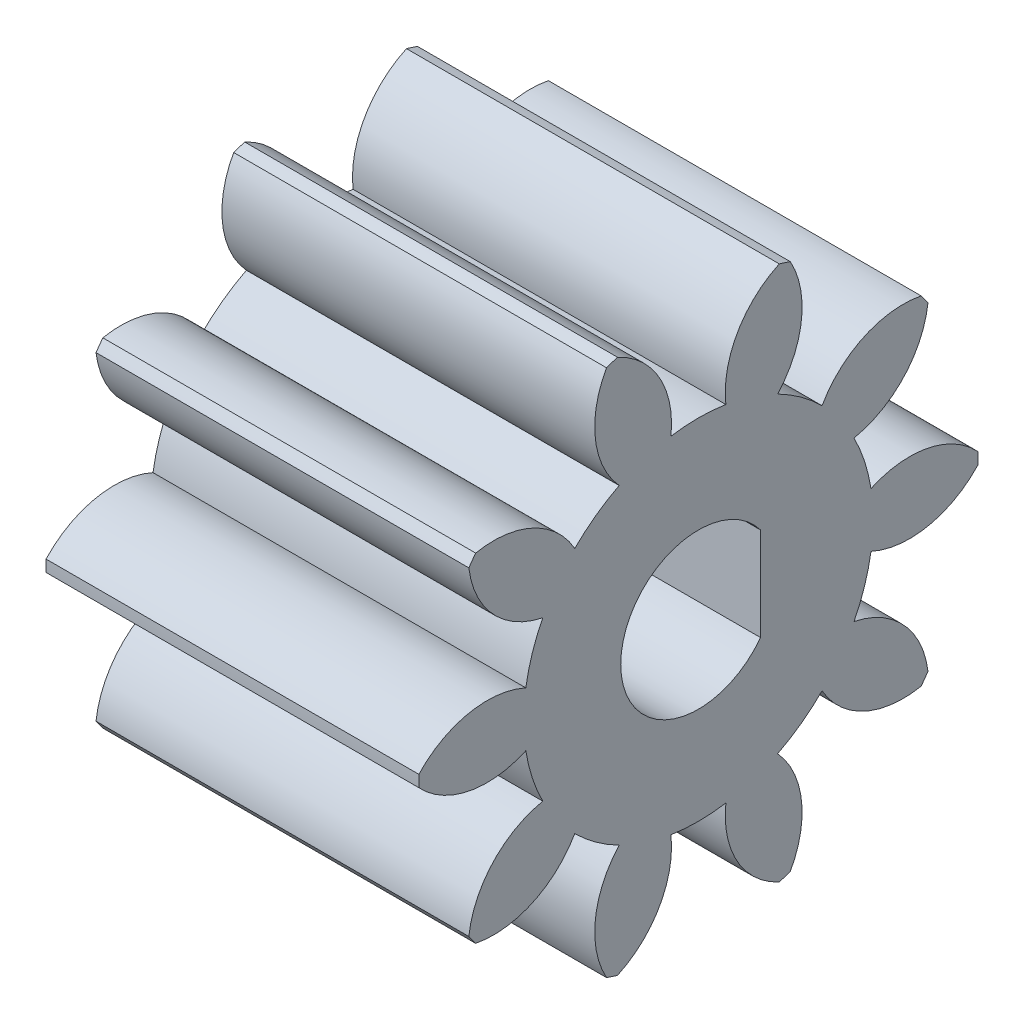
SolidWorks part; units mm, degrees
ref_plane "Plane1" through (0, 0, 0) normal (0, 0, 1) x (1, 0, 0)
ref_plane "Plane2" through (0, 0, 0) normal (0, 1, 0) x (1, 0, 0)
ref_plane "Plane3" through (0, 0, 0) normal (1, 0, 0) x (0, 0, -1)
sketch "HoldingSke" plane through (0, 0, 0) normal (0, 1, 0) x (1, 0, 0)
  line L0 (0, 0) -> (0.6565, -0.1158)
  line L1 (-15, 0) -> (100, 0) construction
  line L2 (0, 0) -> (-2.1039, 2.3779)
  line L3 (0, 0) -> (-11.863, 4.5341)
  line L4 (0, 0) -> (8.5048, 1.4996)
  line L5 (0, 0) -> (-46.8476, -17.4728)
  line L6 (0, 0) -> (-9.9476, -6.7116)
  line L7 (-2.1039, 2.3779) -> (8.6586, 51.2059)
  line L8 (-76.2, 54.61) -> (-75.5, 54.61)
  line L9 (-71.009, 38.7566) -> (-53.1078, 45.2721)
  line L10 (-76.2, 71.12) -> (104.1128, 71.12)
  line L11 (0, 0) -> (-12, 0)
  line L12 (-76.2, 101.6) -> (-76.147, 101.6)
  line L13 (24.9733, 27.94) -> (52.9518, 28.4284)
  line L14 (24.9733, 27.94) -> (24.9743, 27.94)
  line L15 (24.9733, 27.94) -> (100.4006, 29.5858)
  line L16 (-63.627, -1.5) -> (-12.827, -1.5)
  circle A0 centre (0, 0) radius 2
  circle A1 centre (0, 0) radius 5.624
  circle A2 centre (0, 0) radius 37.5
  circle A3 centre (0, 0) radius 2
  dimension "MHD" = 11.248
  dimension "Hub_dia" = 75
  dimension "Bore" = 4
  dimension "MBD" = 4
  dimension "Num_teeth" = 10
  dimension "Pitch" = 0.6667
  dimension "Overall_len" = 50
  dimension "Show_teeth" = 10
  dimension "Thickness" = 12
  dimension "OAL" = 50.0001
  dimension "T_dim" = 0.7
  dimension "Ap" = 20
  dimension "H" = 19.05
  dimension "Pitch_radius" = 180.3128
  dimension "Width" = 12
  dimension "Backlash" = 0.053
  dimension "Addendum_fac" = 1
  dimension "Dedendum_fac" = 1.25
  dimension "Clearance_fac" = 0.25
  dimension "Dedendum_add" = 0.001
  dimension "Module" = 1.5
sketch "BasProSke" plane through (0, 0, 0) normal (0, 1, 0) x (1, 0, 0)
  line L0 (-10, 0) -> (60, 0) construction
  line L1 (0, 0) -> (0, 9)
  line L2 (0, 0) -> (12, 0)
  line L3 (12, 0) -> (12, 9)
  line L4 (12, 9) -> (0, 9)
  dimension "Thickness" = 12
  dimension "Diameter" = 18
revolve "Base-Revolve" add sketch "BasProSke" angle 360 about L0
sketch "TooCutSke" plane through (0, 0, 0) normal (1, 0, 0) x (0, 0, -1)
  line L1 (0, 0) -> (0, 107) construction
  line L2 (0, 0) -> (-1.2658, 7.3924) construction
  line L3 (0, 0) -> (-4.5869, 14.117) construction
  line L4 (-1.2658, 7.3924) -> (-2.2934, 7.0585) construction
  arc A0 (0.8839, 5.5541) -> (-0.8839, 5.5541) centre (0, 0) ccw
  arc A1 (2.6378, 8.6313) -> (-2.6378, 8.6313) centre (0, 0) ccw
  circle A2 centre (0, 0) radius 7.5 construction
  circle A3 centre (0, 0) radius 7.0477 construction
  arc A4 (-0.8839, 5.5541) -> (-2.6378, 8.6313) centre (-3.8646, 5.8936) ccw
  arc A5 (2.6378, 8.6313) -> (0.8839, 5.5541) centre (3.8646, 5.8936) ccw
  dimension "Root_dia" = 11.248
  dimension "Overcut_dia" = 18.0508
  dimension "Pitch_dia" = 15
  dimension "Base_dia" = 14.0954
  dimension "Flank_rad" = 3
  dimension "Half_ang" = 18
  dimension "Half_CT" = 1.0805
extrude "ToothCut" cut sketch "TooCutSke" along normal through all
fillet "Breaks" [suppressed] radius 0.03
fillet "RootFillets" [suppressed] radius 0.376
pattern_circular "TeethCuts" count 10 every 36 about axis through (-10, 0, 0) along (1, 0, 0) of "ToothCut", "RootFillets", "Breaks"
sketch "HubNeaOneSke" plane through (0, 0, 0) normal (-1, 0, 0) x (0, 0, 1)
  circle A0 centre (0, 0) radius 5.624
  dimension "Diameter" = 11.248
extrude "HubNearOne" [suppressed] add sketch "HubNeaOneSke" along normal blind 38.0001
sketch "HubNeaBotSke" plane through (0, 0, 0) normal (-1, 0, 0) x (0, 0, 1)
  circle A0 centre (0, 0) radius 5.624
  dimension "Diameter" = 11.248
extrude "HubNearBoth" [suppressed] add sketch "HubNeaBotSke" along normal blind 19
ref_plane "FarPln" through (12, 0, 0) normal (1, 0, 0) x (0, 0, -1)
sketch "HubFarSke" plane through (12, 0, 0) normal (1, 0, 0) x (0, 0, -1)
  circle A0 centre (0, 0) radius 5.624
  dimension "Diameter" = 11.248
extrude "HubFar" [suppressed] add sketch "HubFarSke" along normal blind 19
sketch "BorSke" plane through (0, 0, 0) normal (1, 0, 0) x (0, 0, -1)
  circle A0 centre (0, 0) radius 2
  dimension "Diameter" = 4
extrude "Bore" cut sketch "BorSke" along normal mid plane 100.0001
sketch "KeySke" plane through (0, 0, 0) normal (1, 0, 0) x (0, 0, -1)
  line L0 (-0.8, 0) -> (-0.8, 2.7)
  line L1 (-0.8, 2.7) -> (0.8, 2.7)
  line L2 (0.8, 2.7) -> (0.8, 0)
  line L3 (0, 0) -> (0, 34) construction
  line L4 (-0.8, 0) -> (0.8, 0)
  dimension "Offset" = 2.7
  dimension "Width" = 1.6
extrude "Keyway" [suppressed] cut sketch "KeySke" along normal mid plane 100.0001
pattern_circular "Keyway2" [suppressed] count 2 every 90 about axis through (-10, 0, 0) along (1, 0, 0)
sketch "Sketch1" plane through (12, 0, 0) normal (1, 0, 0) x (0, 0, -1)
  line L0 (2, 1.5) -> (2, -1.5)
  line L1 (-2.5, 0) -> (-2.5, -13.2605) construction
  line L2 (-2.5, -13.2605) -> (-2.5, 14.3098) construction
  arc A0 (2, 1.5) -> (2, -1.5) centre (0, 0) ccw
  point P7 (0, 0)
  point P8 (-2.5, 0)
  point P9 (0, 0)
  dimension "D1" = 5
  dimension "D2" = 4.5
extrude "Cut-Extrude1" cut sketch "Sketch1" against normal blind 18
equation "' \"Module@HoldingSke\" = 6.35"
equation "' \"Num_teeth@HoldingSke\" = 12"
equation "' \"Ap@HoldingSke\" =  20"
equation "' \"Ap@HoldingSke\" = 20"
equation "' \"Width@HoldingSke\" = 0.5 * 25.4"
equation "' \"Hub_dia@HoldingSke\"= 1 * 25.4"
equation "' \"Hub_dia@HoldingSke\" = 1 * 25.4"
equation "' \"Overall_len@HoldingSke\" = 1.0 * 25.4"
equation "' \"Bore@HoldingSke\" = 0.75 * 25.4"
equation "' \"T_dim@HoldingSke\" = 0.1 * 25.4"
equation "' \"Width@KeySke\" = 0.25 * 25.4"
equation "' \"Show_teeth@HoldingSke\" = 13"
equation "' \"Backlash@HoldingSke\" = 0.009 * 25.4"
equation "' \"Addendum_fac@HoldingSke\" = 1.0"
equation "' \"Dedendum_fac@HoldingSke\" = 1.25"
equation "' \"Dedendum_add@HoldingSke\" = 0.00005 * 25.4"
equation "' \"Clearance_fac@HoldingSke\" = 0.25"
equation "\"Pitch@HoldingSke\" = 1 / \"Module@HoldingSke\""
equation "\"Overcut_dia@TooCutSke\" = (\"Num_teeth@HoldingSke\" + 2 * \"Addendum_fac@HoldingSke\") / \"Pitch@HoldingSke\" + 0.002 * 25.4"
equation "\"Pitch_dia@TooCutSke\" = \"Num_teeth@HoldingSke\" / \"Pitch@HoldingSke\""
equation "\"Base_dia@TooCutSke\" = \"Num_teeth@HoldingSke\" / \"Pitch@HoldingSke\" * cos((\"Ap@HoldingSke\"  * 3.14159265 / 180))"
equation "\"Root_dia@TooCutSke\" = (\"Num_teeth@HoldingSke\" + 2) / \"Pitch@HoldingSke\" - 2 * (\"Addendum_fac@HoldingSke\" + \"Dedendum_fac@HoldingSke\") / \"Pitch@HoldingSke\" - \"Dedendum_add@HoldingSke\" * 2"
equation "\"Half_ang@TooCutSke\" = 180 / \"Num_teeth@HoldingSke\""
equation "\"Half_CT@TooCutSke\" = \"Num_teeth@HoldingSke\" / \"Pitch@HoldingSke\" * sin((3.14159265 / 2 / \"Num_teeth@HoldingSke\")) / 2 - 7 * \"Backlash@HoldingSke\" / 4"
equation "\"Flank_rad@TooCutSke\" = \"Num_teeth@HoldingSke\" / \"Pitch@HoldingSke\" / 5"
equation "\"Radius@RootFillets\" = \"Clearance_fac@HoldingSke\" / \"Pitch@HoldingSke\" + \"Dedendum_add@HoldingSke\""
equation "\"Break_rad@Breaks\" = 0.02 / \"Pitch@HoldingSke\""
equation "\"Thickness@HoldingSke\" = \"Width@HoldingSke\""
equation "\"OAL@HoldingSke\" = \"Thickness@HoldingSke\""
equation "\"MHD@HoldingSke\" = (\"Num_teeth@HoldingSke\" + 2) / \"Pitch@HoldingSke\" - 2 * (\"Addendum_fac@HoldingSke\" + \"Dedendum_fac@HoldingSke\")  / \"Pitch@HoldingSke\" - \"Dedendum_add@HoldingSke\" * 2"
equation "\"MBD@HoldingSke\" = (\"Num_teeth@HoldingSke\" + 2) / \"Pitch@HoldingSke\" - 2 * (\"Addendum_fac@HoldingSke\" + \"Dedendum_fac@HoldingSke\")  / \"Pitch@HoldingSke\" - \"Dedendum_add@HoldingSke\" * 2 - 0.002 * 25.4"
equation "\"MHD@HoldingSke\" = ((sgn( \"MHD@HoldingSke\" - \"Hub_dia@HoldingSke\" )-1)*( \"MHD@HoldingSke\" - \"Hub_dia@HoldingSke\" ))/-2+ \"Hub_dia@HoldingSke\""
equation "\"MBD@HoldingSke\" = ((sgn( \"MBD@HoldingSke\" - \"Bore@HoldingSke\" )-1)*( \"MBD@HoldingSke\" - \"Bore@HoldingSke\" ))/-2+ \"Bore@HoldingSke\""
equation "\"OAL@HoldingSke\" = ((sgn( \"OAL@HoldingSke\" - \"Overall_len@HoldingSke\" )+1)*( \"OAL@HoldingSke\" - \"Overall_len@HoldingSke\" ))/2 + \"Overall_len@HoldingSke\" + 0.000002 * 25.4"
equation "\"Num_teeth@TeethCuts\" = int( \"Show_teeth@HoldingSke\" ) + 1"
equation "\"Num_teeth@TeethCuts\" = ((sgn( \"Num_teeth@TeethCuts\" - \"Num_teeth@HoldingSke\" )-1)*( \"Num_teeth@TeethCuts\" - \"Num_teeth@HoldingSke\" ))/-2+ \"Num_teeth@HoldingSke\""
equation "\"Num_teeth@TeethCuts\" = ((sgn( \"Num_teeth@TeethCuts\" - 2.0)+1)*( \"Num_teeth@TeethCuts\" - 2.0))/2 +2.0"
equation "\"Angle@TeethCuts\" = 360.0 / \"Num_teeth@HoldingSke\""
equation "\"Diameter@BasProSke\" = (\"Num_teeth@HoldingSke\" + 2 * \"Addendum_fac@HoldingSke\") / \"Pitch@HoldingSke\""
equation "\"Thickness@BasProSke\"  = \"Thickness@HoldingSke\""
equation "' \"Fillet_rad@BasProSke\" =  \"Thickness@HoldingSke\" * 0.05"
equation "' \"Fillet_rad@BasProSke\" = \"Thickness@HoldingSke\" * 0.05"
equation "\"MHD@HoldingSke\" = ((sgn( \"MHD@HoldingSke\" - \"Root_dia@TooCutSke\" )-1)*( \"MHD@HoldingSke\" - \"Root_dia@TooCutSke\" ))/-2+ \"Root_dia@TooCutSke\""
equation "\"Diameter@HubNeaOneSke\" = \"MHD@HoldingSke\""
equation "\"Length@HubNearOne\" = \"OAL@HoldingSke\" - \"Thickness@BasProSke\""
equation "\"Diameter@HubNeaBotSke\" = \"MHD@HoldingSke\""
equation "\"Length@HubNearBoth\" = ( \"OAL@HoldingSke\" - \"Thickness@BasProSke\" ) / 2.0"
equation "\"Thickness@FarPln\" = \"Thickness@BasProSke\""
equation "\"Diameter@HubFarSke\" = \"MHD@HoldingSke\""
equation "\"Length@HubFar\" = ( \"OAL@HoldingSke\" - \"Thickness@BasProSke\" ) / 2.0"
equation "\"Diameter@BorSke\" = \"MBD@HoldingSke\""
equation "\"D1@Bore\" = \"OAL@HoldingSke\" * 2.0"
equation "\"D1@Keyway\" = \"OAL@HoldingSke\" * 2.0"
equation "\"Offset@KeySke\" = \"T_dim@HoldingSke\" + \"MBD@HoldingSke\" / 2.0"
